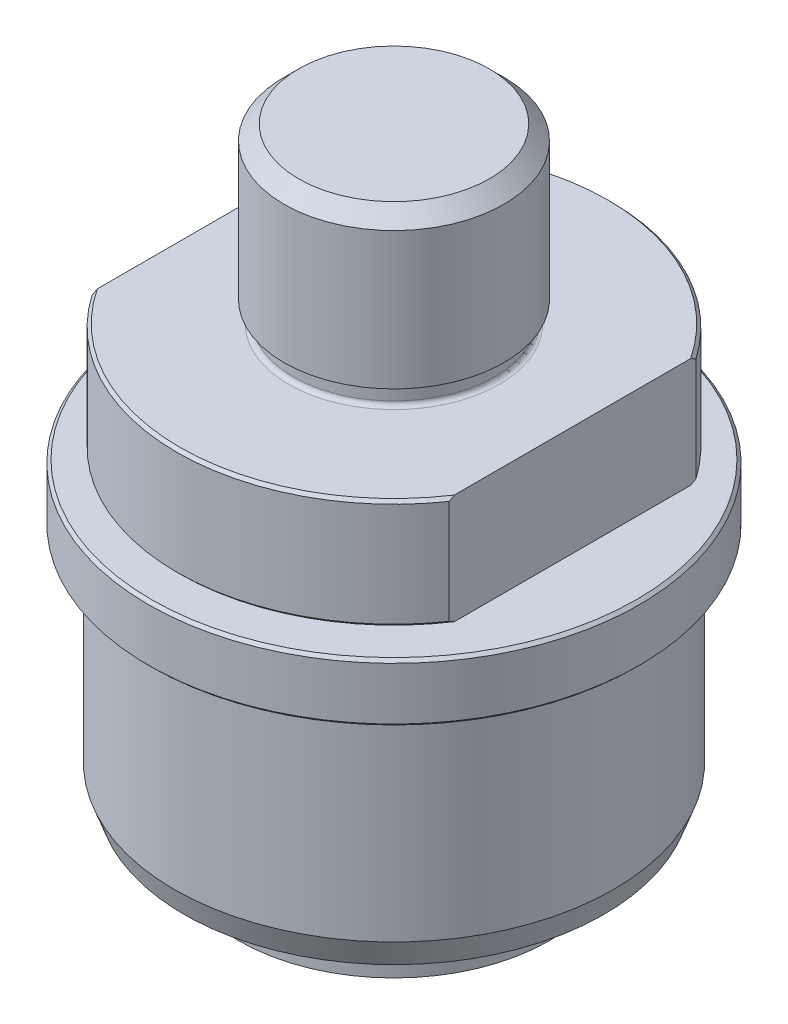
SolidWorks part; units mm, degrees
ref_plane "Front Plane" through (0, 0, 0) normal (0, 0, 1) x (1, 0, 0)
ref_plane "Top Plane" through (0, 0, 0) normal (0, 1, 0) x (1, 0, 0)
ref_plane "Right Plane" through (0, 0, 0) normal (1, 0, 0) x (0, 0, -1)
sketch "Sketch1" plane through (0, 0, 0) normal (0, 0, 1) x (1, 0, 0)
  line L0 (0, 29.972) -> (0, -49.1744)
  line L1 (0, 29.972) -> (19.05, 29.972)
  line L2 (19.05, 29.972) -> (19.05, 3.683)
  line L3 (18.2245, 0) -> (37.5793, 0)
  line L4 (37.5793, 0) -> (37.5793, -18.9992)
  line L5 (37.5793, -18.9992) -> (26.8605, -18.9992)
  line L6 (26.8605, -18.9992) -> (26.8605, -73.6346)
  line L7 (26.8605, -79.121) -> (21.5646, -79.121)
  line L8 (0, 29.972) -> (0, 50.8132) construction
  line L9 (19.05, 3.683) -> (17.4625, 3.683)
  line L10 (17.4625, 3.683) -> (17.4625, 0.762)
  line L11 (20.0406, -77.597) -> (20.0406, -60.579)
  line L12 (20.0406, -60.579) -> (8.636, -49.1744)
  line L13 (8.636, -49.1744) -> (0, -49.1744)
  line L14 (26.8605, -76.6826) -> (26.8605, -79.121)
  arc A0 (26.8605, -73.6346) -> (26.8605, -76.6826) centre (26.8605, -75.1586) ccw
  arc A1 (21.5646, -79.121) -> (20.0406, -77.597) centre (21.5646, -77.597) cw
  arc A2 (18.2245, 0) -> (17.4625, 0.762) centre (18.2245, 0.762) cw
  dimension "D14" = 1.524
  dimension "D15" = 1.524
  dimension "D16" = 0.762
  dimension "D1" = 38.1
  dimension "D2" = 29.972
  dimension "D3" = 18.9992
  dimension "D4" = 79.121
  dimension "D5" = 53.721
  dimension "D6" = 75.1586
  dimension "D7" = 3.683
  dimension "D8" = 34.925
  dimension "D9" = 40.0812
  dimension "D10" = 18.542
  dimension "D11" = 45
  dimension "D12" = 17.272
  dimension "D13" = 2.4384
revolve "Revolve1" add sketch "Sketch1" angle 360 about L8
chamfer "Chamfer1" distance 0.508 angle 45 2 edges at (0, -18.9992, -37.5793) (0, 0, -37.5793)
chamfer "Chamfer2" distance 2.54 angle 45 1 edges at (0, 29.972, -19.05)
sketch "Sketch4" plane through (0, 0, 0) normal (0, 1, 0) x (1, 0, 0)
  line L0 (-30.9118, 21.3697) -> (-30.9118, -21.3697)
  line L1 (30.9118, 21.3697) -> (30.9118, -21.3697)
  circle A0 centre (0, 0) radius 37.5793 construction
  arc A1 (30.9118, -21.3697) -> (30.9118, 21.3697) centre (0, 0) ccw
  arc A2 (-30.9118, 21.3697) -> (-30.9118, -21.3697) centre (0, 0) ccw
  dimension "D1" = 30.9118
  dimension "D2" = 30.9118
extrude "Cut-Extrude1" cut sketch "Sketch4" against normal through all
sketch "Sketch2" plane through (0, 0, 0) normal (0, 0, 1) x (1, 0, 0)
  line L0 (26.9113, -20.3708) -> (26.9113, -64.3636)
  line L1 (32.1056, -70.4088) -> (36.3597, -70.4088)
  line L2 (36.3597, -70.4088) -> (38.0238, -65.8368)
  line L3 (38.0238, -65.8368) -> (38.0238, -31.242)
  line L4 (38.7858, -30.48) -> (42.5069, -30.48)
  line L5 (42.5069, -30.48) -> (42.5069, -20.3708)
  line L6 (42.5069, -20.3708) -> (26.9113, -20.3708)
  line L7 (0, 0) -> (0, 33.0062) construction
  line L8 (37.0713, 0) -> (-37.0713, 0) construction
  line L9 (26.8605, -73.6346) -> (26.8605, -18.9992) construction
  line L11 (32.1056, -70.4088) -> (32.1056, -65.3796)
  line L12 (31.0896, -64.3636) -> (26.9113, -64.3636)
  line L13 (26.8605, -73.6346) -> (-26.8605, -73.6346) construction
  line L14 (-26.8605, -79.121) -> (26.8605, -79.121) construction
  arc A0 (32.1056, -65.3796) -> (31.0896, -64.3636) centre (31.0896, -65.3796) ccw
  arc A1 (38.0238, -31.242) -> (38.7858, -30.48) centre (38.7858, -31.242) cw
  dimension "D13" = 1.016
  dimension "D14" = 0.762
  dimension "D1" = 50.038
  dimension "D2" = 10.1092
  dimension "D3" = 76.0476
  dimension "D4" = 85.0138
  dimension "D5" = 4.572
  dimension "D6" = 20
  dimension "D7" = 72.7195
  dimension "D8" = 30.48
  dimension "D9" = 0.0508
  dimension "D10" = 9.271
  dimension "D11" = 8.7122
  dimension "D12" = 64.2112
revolve "Revolve2" add sketch "Sketch2" angle 360 about L7
chamfer "Chamfer3" distance 0.508 angle 45 2 edges at (0, -20.3708, -42.5069) (0, -30.48, -42.5069)
sketch "Sketch3" plane through (0, 0, 0) normal (0, 0, 1) x (1, 0, 0)
  line L1 (0, 0) -> (0, -31.4929) construction
  circle A0 centre (26.8605, -75.1586) radius 1.4732
  arc A2 (26.8605, -73.6346) -> (26.8605, -76.6826) centre (26.8605, -75.1586) ccw construction
  dimension "D1" = 0.0508
revolve "Revolve3" add sketch "Sketch3" angle 330 about L1
